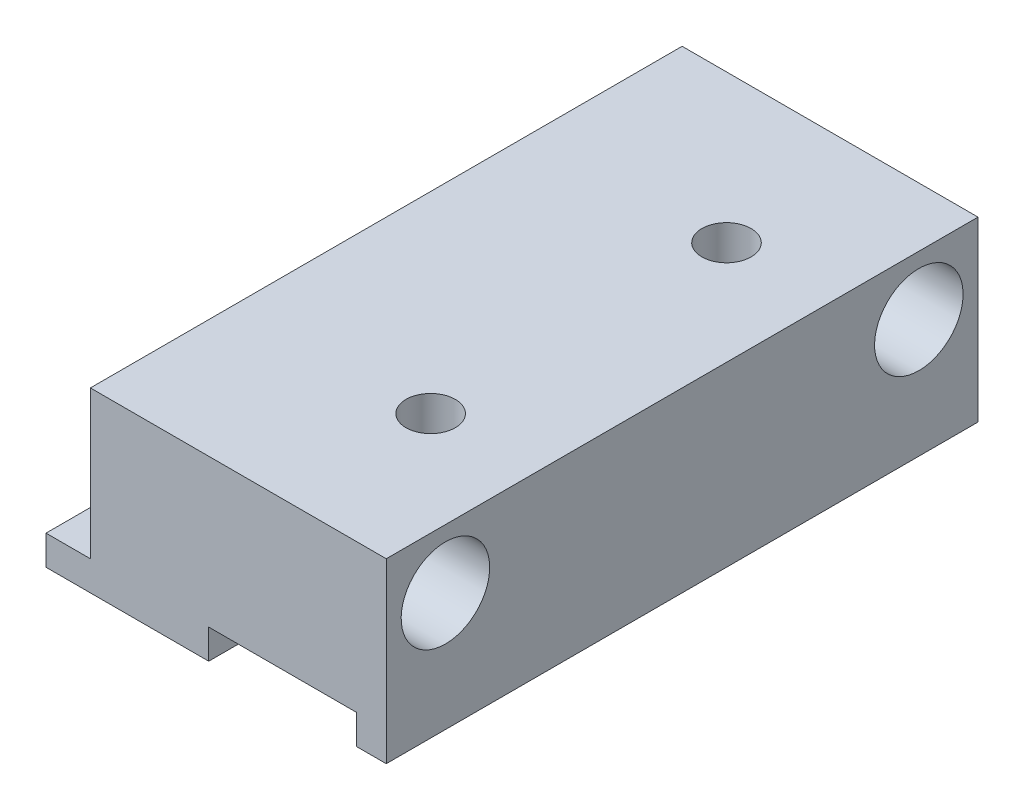
SolidWorks part; units mm, degrees
ref_plane "Front Plane" through (0, 0, 0) normal (0, 0, 1) x (1, 0, 0)
ref_plane "Top Plane" through (0, 0, 0) normal (0, 1, 0) x (1, 0, 0)
ref_plane "Right Plane" through (0, 0, 0) normal (1, 0, 0) x (0, 0, -1)
sketch "Sketch1" plane through (0, 0, 0) normal (0, 0, 1) x (1, 0, 0)
  line L0 (12.7273, -8.5682) -> (14.7273, -8.5682)
  line L1 (-5.2727, 3.4318) -> (14.7273, 3.4318)
  line L2 (-5.2727, 3.4318) -> (-5.2727, -6.5682)
  line L3 (-8.2727, -8.5682) -> (2.7273, -8.5682)
  line L4 (14.7273, 3.4318) -> (14.7273, -8.5682)
  line L6 (12.7273, -8.5682) -> (12.7273, -6.5682)
  line L7 (12.7273, -6.5682) -> (2.7273, -6.5682)
  line L8 (2.7273, -8.5682) -> (2.7273, -6.5682)
  line L11 (-5.2727, -6.5682) -> (-8.2727, -6.5682)
  line L12 (-8.2727, -8.5682) -> (-8.2727, -6.5682)
  point P11 (0, 0)
  point P12 (0, 0)
  point P13 (-8.1418, -8.5682)
  dimension "D1" = 2
  dimension "D2" = 2
  dimension "D3" = 20
  dimension "D4" = 2
  dimension "D5" = 10
  dimension "D6" = 12
  dimension "D7" = 3
extrude "Boss-Extrude1" add sketch "Sketch1" along normal blind 40
sketch "Sketch2" plane through (-5.2727, 0, 0) normal (-1, 0, 0) x (0, 0, 1)
  line L0 (40, 3.4318) -> (0, 3.4318) construction
  line L1 (40, 3.4318) -> (40, -6.5682) construction
  circle A0 centre (4, -0.5682) radius 2.9912
  circle A1 centre (36, -0.5682) radius 2.9912
  dimension "D1" = 4
  dimension "D2" = 4
  dimension "D3" = 4
  dimension "D4" = 36
extrude "Cut-Extrude1" cut sketch "Sketch2" against normal through all
sketch "Sketch3" plane through (0, 3.4318, 0) normal (0, 1, 0) x (1, 0, 0)
  line L0 (14.7273, 0) -> (-5.2727, 0) construction
  line L1 (14.7273, -40) -> (-5.2727, -40) construction
  line L3 (14.7273, -40) -> (14.7273, 0) construction
  circle A0 centre (7.7273, -30) radius 1.6645
  circle A1 centre (7.7273, -10) radius 1.6645
  point P4 (0, 0)
  dimension "D1" = 10
  dimension "D2" = 10
  dimension "D3" = 7
extrude "Cut-Extrude2" cut sketch "Sketch3" against normal blind 40
